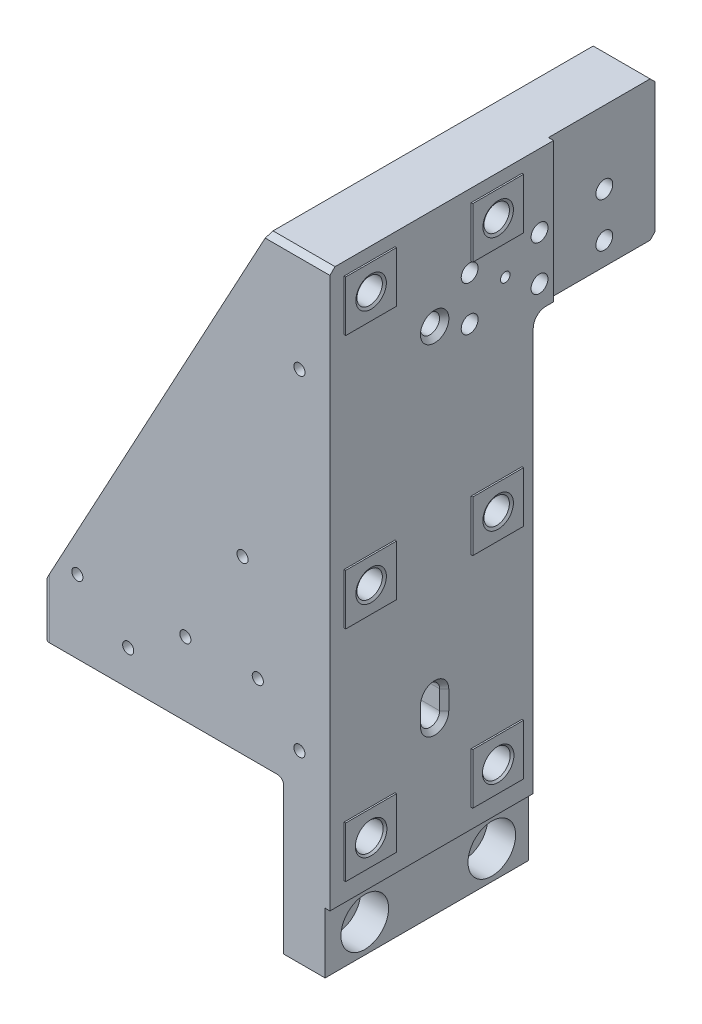
SolidWorks part; units mm, degrees
material "6061-T6 Al"
ref_plane "XY" through (0, 0, 0) normal (0, 0, 1) x (1, 0, 0)
ref_plane "XZ" through (0, 0, 0) normal (0, 1, 0) x (1, 0, 0)
ref_plane "YZ" through (0, 0, 0) normal (1, 0, 0) x (0, 0, -1)
sketch "Sketch1" plane through (0, 0, 0) normal (0, 0, 1) x (1, 0, 0)
  line L1 (0, 0) -> (25.4, 0)
  line L2 (0, 0) -> (0, 309.372)
  line L3 (0, 309.372) -> (25.4, 309.372)
  line L4 (25.4, 0) -> (25.4, 309.372)
  dimension "D1" = 309.372
  dimension "D2" = 25.4
extrude "Extrude1" add sketch "Sketch1" along normal blind 101.6
sketch "Sketch2" plane through (0, 0, 101.6) normal (0, 0, 1) x (1, 0, 0)
  line L0 (0, 309.372) -> (-6.35, 309.372)
  line L1 (-6.35, 309.372) -> (-118.745, 101.6)
  line L2 (-118.745, 101.6) -> (-118.745, 76.2)
  line L3 (-118.745, 76.2) -> (0, 76.2)
  line L4 (0, 76.2) -> (0, 309.372)
  line L5 (0, 309.372) -> (0, 0) construction
  line L6 (0, 0) -> (25.4, 0) construction
  dimension "D1" = 118.745
  dimension "D2" = 6.35
  dimension "D3" = 25.4
  dimension "D4" = 76.2
extrude "Extrude2" add sketch "Sketch2" against normal blind 53.975
sketch "Sketch7" plane through (0, 0, 0) normal (0, 0, -1) x (-1, 0, 0)
  line L0 (0, 76.2) -> (22.225, 76.2)
  line L1 (118.745, 76.2) -> (0, 76.2) construction
  line L2 (22.225, 76.2) -> (22.225, 280.0257)
  line L3 (0, 309.372) -> (0, 0) construction
  line L4 (0, 76.2) -> (0, 309.372)
  line L5 (0, 309.372) -> (6.35, 309.372)
  line L6 (6.35, 309.372) -> (22.225, 280.0257)
  line L7 (6.35, 309.372) -> (118.745, 101.6) construction
  dimension "D1" = 22.225
extrude "Extrude3" add sketch "Sketch7" against normal up to surface (47.625 mm away) up to face at (-48.133, 151.2316, 47.625)
sketch "Sketch3" plane through (0, 0, 101.6) normal (0, 0, 1) x (1, 0, 0)
  line L1 (25.4, 0) -> (22.225, 0)
  line L2 (25.4, 0) -> (25.4, 31.75)
  line L3 (25.4, 31.75) -> (22.225, 31.75)
  line L4 (22.225, 0) -> (22.225, 31.75)
  dimension "D1" = 31.75
  dimension "D2" = 3.175
extrude "Cut-Extrude1" cut sketch "Sketch3" against normal through all
hole_wizard "Lateral Holes CBORE for 1/2 Socket Head Cap Screw2" positions "Sketch40" profile "Sketch39" counterbore size "1/2" standard "Ansi Inch" end condition up to next
sketch "Sketch40" plane through (22.225, 0, 0) normal (1, 0, 0) x (0, 0, -1)
  line L0 (-101.6, 31.75) -> (-101.6, 309.372) construction
  line L1 (-101.6, 15.875) -> (0, 15.875) construction
  line L2 (-101.6, 31.75) -> (-101.6, 0) construction
  line L3 (0, 0) -> (0, 31.75) construction
  line L5 (0, 0) -> (-101.6, 0) construction
  point P0 (-81.788, 15.875)
  point P3 (-18.288, 15.875)
  dimension "D1" = 19.812
  dimension "D2" = 63.5
  dimension "D3" = 15.875
sketch "Sketch39" plane through (22.225, 15.875, 81.788) normal (0, 1, 0) x (0, 0, -1)
  line L0 (0, 0) -> (0, 22.225)
  line L1 (6.9469, 21.2979) -> (7.874, 22.225)
  line L2 (6.9469, 21.2979) -> (6.9469, 13.97)
  line L3 (6.9469, 13.97) -> (11.9126, 13.97)
  line L4 (11.9126, 13.97) -> (11.9126, 0)
  line L5 (11.9126, 0) -> (0, 0)
  line L11 (0, -6.35) -> (0, 107.95) construction
  line L12 (7.874, 22.225) -> (0, 22.225)
  line L13 (-6.9469, 21.2979) -> (-7.874, 22.225) construction
  dimension "Thru Hole Dia." = 13.8938
  dimension "Thru Hole Depth" = 22.225
  dimension "C'Bore Dia." = 23.8252
  dimension "C'Bore Depth" = 13.97
  dimension "Far C'Sink Dia." = 15.748
  dimension "Far C'Sink Angle" = 90
hole_wizard "Lateral Holes 1/2 Clearance Hole1" positions "Sketch42" profile "Sketch41" hole size "1/2" standard "Ansi Inch" end condition up to next
sketch "Sketch42" plane through (25.4, 0, 0) normal (1, 0, 0) x (0, 0, -1)
  line L0 (-101.6, 53.975) -> (0, 53.975) construction
  line L1 (-101.6, 31.75) -> (-101.6, 309.372) construction
  line L2 (0, 31.75) -> (0, 309.372) construction
  line L4 (0, 0) -> (-101.6, 0) construction
  point P0 (-18.288, 53.975)
  point P10 (-81.788, 53.975)
  dimension "D1" = 19.812
  dimension "D2" = 63.5
  dimension "D3" = 53.975
sketch "Sketch41" plane through (25.4, 53.975, 18.288) normal (0, 1, 0) x (0, 0, -1)
  line L0 (0, 0) -> (0, 25.4)
  line L1 (0, 25.4) -> (7.874, 25.4)
  line L2 (6.9456, 24.4716) -> (6.9456, 0.9284)
  line L3 (6.9456, 0.9284) -> (7.874, 0)
  line L5 (7.874, 0) -> (0, 0)
  line L6 (-6.9456, 0.9284) -> (-7.874, 0) construction
  line L7 (7.874, 25.4) -> (6.9456, 24.4716)
  line L8 (-7.874, 25.4) -> (-6.9456, 24.4716) construction
  line L11 (0, -6.35) -> (0, 107.95) construction
  dimension "Thru Hole Dia." = 13.8913
  dimension "Thru Hole Depth" = 25.4
  dimension "Near C'Sink Dia." = 15.748
  dimension "Near C'Sink Angle" = 90
  dimension "Far C'Sink Dia." = 15.748
  dimension "Far C'Sink Angle" = 90
hole_wizard "Lateral Holes 1/2-13 Tapped Hole1" positions "Sketch48" profile "Sketch47" tap size "1/2-13" standard "Ansi Inch"
sketch "Sketch48" plane through (25.4, 0, 0) normal (1, 0, 0) x (0, 0, -1)
  line L0 (-101.6, 290.322) -> (0, 290.322) construction
  line L1 (-101.6, 31.75) -> (-101.6, 309.372) construction
  line L2 (0, 31.75) -> (0, 309.372) construction
  line L6 (-101.6, 53.975) -> (0, 53.975) construction
  point P0 (-81.788, 290.322)
  point P14 (-18.288, 290.322)
  point P18 (-81.788, 163.322)
  point P20 (-18.288, 163.322)
  dimension "D1" = 236.347
  dimension "D2" = 19.812
  dimension "D3" = 63.5
  dimension "D4" = 127
sketch "Sketch47" plane through (25.4, 290.322, 81.788) normal (0, 1, 0) x (0, 0, -1)
  line L0 (0, 0) -> (0, 54.0195)
  line L1 (0, 54.0195) -> (5.3581, 50.8)
  line L2 (5.3581, 50.8) -> (5.3581, 38.1)
  line L3 (5.3581, 38.1) -> (6.35, 38.1)
  line L5 (6.35, 38.1) -> (6.35, 0.7332)
  line L6 (6.35, 0.7332) -> (7.62, 0)
  line L7 (7.62, 0) -> (0, 0)
  line L8 (-6.35, 0.7332) -> (-7.62, 0) construction
  line L10 (0, 54.0195) -> (-5.3581, 50.8) construction
  line L11 (0, -6.35) -> (0, 107.95) construction
  dimension "Tap Drill Dia." = 10.7163
  dimension "Tap Drill Depth" = 50.8
  dimension "Thread Major Dia." = 12.7
  dimension "Thread Depth" = 38.1
  dimension "Near C'Sink Dia." = 15.24
  dimension "Near C'Sink Angle" = 120
  dimension "Drill Angle" = 118
hole_wizard "Bracket Holes 1/2-13 Tapped Hole1" positions "Sketch44" profile "Sketch43" tap size "1/2-13" standard "Ansi Inch"
sketch "Sketch44" plane through (0, 76.2, 0) normal (0, -1, 0) x (1, 0, 0)
  line L0 (-101.6, 101.6) -> (-101.6, 47.625) construction
  line L1 (-118.745, 101.6) -> (0, 101.6) construction
  line L2 (-118.745, 47.625) -> (-22.225, 47.625) construction
  line L4 (-47.625, 101.6) -> (-47.625, 47.625) construction
  line L6 (-101.6, 88.9) -> (-47.625, 88.9) construction
  line L8 (-101.6, 60.325) -> (-47.625, 60.325) construction
  line L10 (0, 101.6) -> (0, 0) construction
  line L14 (25.4, 81.788) -> (-11.43, 81.788) construction
  line L15 (-11.43, 81.788) -> (-11.43, 64.3255) construction
  line L18 (25.4, 18.288) -> (-11.43, 18.288) construction
  line L19 (-11.43, 18.288) -> (-11.43, 35.7505) construction
  line L22 (0, 0) -> (0, 101.6) construction
  point P0 (-101.6, 60.325)
  point P14 (-101.6, 88.9)
  point P16 (-47.625, 88.9)
  point P18 (-47.625, 60.325)
  point P39 (-11.43, 64.3255)
  point P41 (-11.43, 35.7505)
  dimension "D1" = 53.975
  dimension "D2" = 28.575
  dimension "D3" = 47.625
  dimension "D4" = 12.7
  dimension "D5" = 11.43
  dimension "D6" = 28.575
sketch "Sketch43" plane through (-101.6, 76.2, 60.325) normal (1, 0, 0) x (0, 0, -1)
  line L0 (0, 0) -> (0, 47.6695)
  line L1 (0, 47.6695) -> (5.3581, 44.45)
  line L2 (5.3581, 44.45) -> (5.3581, 31.75)
  line L3 (5.3581, 31.75) -> (6.35, 31.75)
  line L5 (6.35, 31.75) -> (6.35, 0.7332)
  line L6 (6.35, 0.7332) -> (7.62, 0)
  line L7 (7.62, 0) -> (0, 0)
  line L8 (-6.35, 0.7332) -> (-7.62, 0) construction
  line L10 (0, 47.6695) -> (-5.3581, 44.45) construction
  line L11 (0, -6.35) -> (0, 107.95) construction
  dimension "Tap Drill Dia." = 10.7163
  dimension "Tap Drill Depth" = 44.45
  dimension "Thread Major Dia." = 12.7
  dimension "Thread Depth" = 31.75
  dimension "Near C'Sink Dia." = 15.24
  dimension "Near C'Sink Angle" = 120
  dimension "Drill Angle" = 118
hole_wizard "Pin Hole 3/8 (0.375) Diameter Hole3" positions "Sketch46" profile "Sketch45" counterbore size "3/8" standard "Ansi Inch"
sketch "Sketch46" plane through (0, 76.2, 0) normal (0, -1, 0) x (1, 0, 0)
  line L0 (-118.745, 101.6) -> (0, 101.6) construction
  line L1 (0, 0) -> (0, 101.6) construction
  point P0 (-76.2, 73.025)
  dimension "D1" = 28.575
  dimension "D2" = 76.2
sketch "Sketch45" plane through (-76.2, 76.2, 73.025) normal (1, 0, 0) x (0, 0, -1)
  line L0 (0, 0) -> (0, 21.9116)
  line L1 (0, 21.9116) -> (4.7625, 19.05)
  line L2 (4.7625, 19.05) -> (4.7625, 3.302)
  line L3 (4.7625, 3.302) -> (4.7879, 3.302)
  line L5 (4.7879, 3.302) -> (4.7879, 0.5461)
  line L6 (4.7879, 0.5461) -> (5.334, 0)
  line L7 (5.334, 0) -> (0, 0)
  line L8 (-4.7879, 0.5461) -> (-5.334, 0) construction
  line L10 (0, 21.9116) -> (-4.7625, 19.05) construction
  line L11 (0, -6.35) -> (0, 107.95) construction
  dimension "Hole Dia." = 9.525
  dimension "Hole Depth" = 19.05
  dimension "C'Bore Dia." = 9.5758
  dimension "C'Bore Depth" = 3.302
  dimension "Near C'Sink Dia." = 10.668
  dimension "Near C'Sink Angle" = 90
  dimension "Drill Angle" = 118
sketch "Sketch49" plane through (25.4, 0, 0) normal (1, 0, 0) x (0, 0, -1)
  line L0 (-101.6, 290.322) -> (0, 290.322) construction
  line L1 (-94.488, 303.022) -> (-69.088, 303.022)
  line L2 (-94.488, 303.022) -> (-94.488, 277.622)
  line L3 (-94.488, 277.622) -> (-69.088, 277.622)
  line L4 (-69.088, 303.022) -> (-69.088, 277.622)
  line L5 (-30.988, 303.022) -> (-5.588, 303.022)
  line L6 (-30.988, 303.022) -> (-30.988, 277.622)
  line L7 (-30.988, 277.622) -> (-5.588, 277.622)
  line L8 (-5.588, 303.022) -> (-5.588, 277.622)
  line L9 (-94.488, 66.675) -> (-69.088, 66.675)
  line L10 (-94.488, 66.675) -> (-94.488, 41.275)
  line L11 (-94.488, 41.275) -> (-69.088, 41.275)
  line L12 (-69.088, 66.675) -> (-69.088, 41.275)
  line L13 (-30.988, 66.675) -> (-5.588, 66.675)
  line L14 (-30.988, 66.675) -> (-30.988, 41.275)
  line L15 (-30.988, 41.275) -> (-5.588, 41.275)
  line L16 (-5.588, 66.675) -> (-5.588, 41.275)
  line L17 (-94.488, 176.022) -> (-69.088, 176.022)
  line L18 (-94.488, 176.022) -> (-94.488, 150.622)
  line L19 (-94.488, 150.622) -> (-69.088, 150.622)
  line L20 (-69.088, 176.022) -> (-69.088, 150.622)
  line L21 (-30.988, 176.022) -> (-5.588, 176.022)
  line L22 (-30.988, 176.022) -> (-30.988, 150.622)
  line L23 (-30.988, 150.622) -> (-5.588, 150.622)
  line L24 (-5.588, 176.022) -> (-5.588, 150.622)
  circle A2 centre (-81.788, 53.975) radius 7.874 construction
  circle A3 centre (-81.788, 53.975) radius 6.9456 construction
  circle A4 centre (-18.288, 53.975) radius 7.874 construction
  point P22 (-94.488, 290.322)
  point P32 (-94.488, 163.322)
  dimension "D8" = 12.7
  dimension "D1" = 12.7
  dimension "D2" = 12.7
  dimension "D3" = 25.4
  dimension "D4" = 25.4
  dimension "D5" = 25.4
  dimension "D6" = 25.4
extrude "Lateral Pads Extrude4" cut sketch "Sketch49" against normal blind 0.762 flip side to cut
hole_wizard "Thru Vent Holes 7/32 (0.21875) Diameter Hole1" positions "Sketch51" profile "Sketch52" hole size "7/32" standard "Ansi Inch" end condition through all
sketch "Sketch51" plane through (0, 0, 101.6) normal (0, 0, 1) x (1, 0, 0)
  line L8 (-118.745, 76.2) -> (0, 76.2) construction
  point P0 (-47.625, 114.3)
  point P17 (-101.6, 114.3)
  point P28 (-76.2, 95.25)
  point P36 (-11.43, 114.3)
  dimension "D1" = 38.1
  dimension "D5" = 19.05
sketch "Sketch52" plane through (-47.625, 114.3, 101.6) normal (1, 0, 0) x (0, -1, 0)
  line L0 (0, 0) -> (0, 101.6)
  line L1 (0, 101.6) -> (2.7781, 101.6)
  line L2 (2.7781, 101.6) -> (2.7781, 0)
  line L5 (2.7781, 0) -> (0, 0)
  line L11 (0, -6.35) -> (0, 107.95) construction
  dimension "Thru Hole Dia." = 5.5562
  dimension "Thru Hole Depth" = 101.6
hole_wizard "Blind Vent Hole 7/32 (0.21875) Diameter Hole3" positions "Sketch76" profile "Sketch75" hole size "7/32" standard "Ansi Inch"
sketch "Sketch76" plane through (0, 0, 101.6) normal (0, 0, 1) x (1, 0, 0)
  line L0 (25.4, 176.022) -> (25.4, 150.622) construction
  point P0 (-19.05, 163.322)
  dimension "D1" = 44.45
sketch "Sketch75" plane through (-19.05, 163.322, 101.6) normal (1, 0, 0) x (0, -1, 0)
  line L0 (0, 0) -> (0, 21.4813)
  line L1 (0, 21.4813) -> (2.7781, 19.812)
  line L2 (2.7781, 19.812) -> (2.7781, 0)
  line L5 (2.7781, 0) -> (0, 0)
  line L10 (0, 21.4813) -> (-2.7781, 19.812) construction
  line L11 (0, -6.35) -> (0, 107.95) construction
  dimension "Hole Dia." = 5.5562
  dimension "Hole Depth" = 19.812
  dimension "Drill Angle" = 118
hole_wizard "Pin Hole 3/8 (0.375) Diameter Hole4" positions "Sketch56" profile "Sketch55" hole size "3/8" standard "Ansi Inch"
sketch "Sketch56" plane through (24.638, 0, 0) normal (1, 0, 0) x (0, 0, -1)
  line L0 (-101.6, 309.372) -> (-101.6, 31.75) construction
  line L2 (0, 309.372) -> (-101.6, 309.372) construction
  point P0 (-49.276, 258.572)
  dimension "D1" = 52.324
  dimension "D2" = 50.8
sketch "Sketch55" plane through (24.638, 258.572, 49.276) normal (0, 1, 0) x (0, 0, -1)
  line L0 (0, 0) -> (0, 21.9169)
  line L1 (0, 21.9169) -> (4.7714, 19.05)
  line L2 (4.7714, 19.05) -> (4.7714, 2.3406)
  line L3 (4.7714, 2.3406) -> (7.112, 0)
  line L5 (7.112, 0) -> (0, 0)
  line L6 (-4.7714, 2.3406) -> (-7.112, 0) construction
  line L10 (0, 21.9169) -> (-4.7714, 19.05) construction
  line L11 (0, -6.35) -> (0, 107.95) construction
  dimension "Hole Dia." = 9.5428
  dimension "Hole Depth" = 19.05
  dimension "Near C'Sink Dia." = 14.224
  dimension "Near C'Sink Angle" = 90
  dimension "Drill Angle" = 118
sketch "Sketch57" plane through (24.638, 0, 0) normal (1, 0, 0) x (0, 0, -1)
  line L0 (-49.276, 98.2345) -> (-49.276, 88.7095) construction
  line L1 (-44.5046, 98.2345) -> (-44.5046, 88.7095)
  line L2 (-54.0474, 98.2345) -> (-54.0474, 88.7095)
  line L4 (-101.6, 309.372) -> (-101.6, 31.75) construction
  line L5 (0, 309.372) -> (-101.6, 309.372) construction
  arc A0 (-44.5046, 98.2345) -> (-54.0474, 98.2345) centre (-49.276, 98.2345) ccw
  arc A1 (-54.0474, 88.7095) -> (-44.5046, 88.7095) centre (-49.276, 88.7095) ccw
  point P2 (-49.276, 93.472)
  dimension "D2" = 4.7714
  dimension "D1" = 9.525
  dimension "D3" = 215.9
  dimension "D4" = 52.324
extrude "Pin Slot Extrude5" cut sketch "Sketch57" against normal blind 19.05
chamfer "Pin Slot Chamfer5" distance 2.286 angle 45 4 edges at (24.638, 93.472, 44.5046) (24.638, 83.9381, 49.276) (24.638, 93.472, 54.0474) (24.638, 103.0059, 49.276)
sketch "Sketch58" plane through (0, 309.372, 0) normal (0, 1, 0) x (1, 0, 0)
  line L0 (24.638, 0) -> (-6.35, 0) construction
  line L1 (-6.731, 0) -> (-22.479, 0)
  line L2 (-6.731, 0) -> (-6.731, -47.625)
  line L3 (-6.731, -47.625) -> (-22.479, -47.625)
  line L4 (-22.479, 0) -> (-22.479, -47.625)
  line L5 (-22.225, -47.625) -> (-118.745, -47.625) construction
  line L6 (24.638, 0) -> (24.638, -101.6) construction
  dimension "D1" = 31.369
  dimension "D2" = 15.748
extrude "Cut-Extrude2" cut sketch "Sketch58" against normal blind 76.2
sketch "Sketch59" plane through (0, 0, 0) normal (0, 0, -1) x (-1, 0, 0)
  line L0 (6.35, 309.372) -> (6.731, 308.6677)
  line L1 (-24.638, 309.372) -> (6.35, 309.372)
  line L2 (-24.638, 309.372) -> (-24.638, 239.522)
  line L3 (-24.638, 239.522) -> (6.731, 239.522)
  line L4 (6.731, 308.6677) -> (6.731, 239.522)
  dimension "D1" = 69.85
extrude "Extrude4" add sketch "Sketch59" along normal blind 63.5
hole_wizard "Tapped Hole for 5/16-18 Helicoil1" positions "Sketch61" profile "Sketch60" tap size "5/16-18" standard "Helicoil® Inch" end condition through all
sketch "Sketch61" plane through (-6.731, 0, 0) normal (-1, 0, 0) x (0, 0, 1)
  point P0 (-38.0746, 273.1008)
  dimension "D1" = 273.1008
  dimension "D2" = 38.0746
sketch "Sketch60" plane through (-6.731, 273.1008, -38.0746) normal (0, 1, 0) x (0, 0, 1)
  line L0 (0, 0) -> (0, 32.131)
  line L1 (0, 32.131) -> (4.2164, 32.131)
  line L3 (4.2164, 32.131) -> (4.2164, 19.2634)
  line L4 (4.9327, 19.2634) -> (4.2164, 19.2634)
  line L5 (4.9327, 19.2634) -> (4.9327, 0.635)
  line L6 (4.9327, 0.635) -> (5.5677, 0)
  line L7 (5.5677, 0) -> (0, 0)
  line L8 (-4.9327, 0.635) -> (-5.5677, 0) construction
  line L11 (0, -6.35) -> (0, 107.95) construction
  dimension "Thru Tap Drill Dia." = 8.4328
  dimension "Thru Tap Drill Depth" = 32.131
  dimension "Thread Major Dia." = 9.8654
  dimension "Thread Depth" = 19.2634
  dimension "Near C'Sink Dia." = 11.1354
  dimension "Near C'Sink Angle" = 90
pattern_linear "LPattern1" count 3 spacing 34.925 along (0, 0, 1) count 2 spacing 22.225 along (0, -1, 0) of "Tapped Hole for 5/16-18 Helicoil1"
chamfer "Chamfer7" distance 2.54 angle 45 4 edges at (8.9535, 239.522, -63.5) (9.144, 309.372, -63.5) (9.144, 309.372, 101.6) (-14.478, 233.172, 0)
sketch "Sketch62" plane through (24.638, 0, 0) normal (1, 0, 0) x (0, 0, -1)
  line L0 (60.96, 309.372) -> (-99.06, 309.372) construction
  line L1 (63.5, 309.372) -> (10.16, 309.372)
  line L2 (63.5, 309.372) -> (63.5, 239.522)
  line L3 (63.5, 239.522) -> (10.16, 239.522)
  line L4 (10.16, 309.372) -> (10.16, 239.522)
  line L5 (60.96, 239.522) -> (0, 239.522) construction
  line L6 (63.5, 306.832) -> (63.5, 242.062) construction
  dimension "D1" = 53.34
extrude "Extrude5" cut sketch "Sketch62" against normal blind 2.54
hole_wizard "7/32 (0.21875) Diameter Hole2" positions "Sketch67" profile "Sketch66" hole size "7/32" standard "Ansi Inch"
sketch "Sketch67" plane through (0, 0, 101.6) normal (0, 0, 1) x (1, 0, 0)
  line L0 (9.398, 258.572) -> (9.398, 93.472) construction
  line L2 (24.638, 306.832) -> (24.638, 31.75) construction
  point P0 (9.398, 258.572)
  point P1 (9.398, 93.472)
  dimension "D1" = 15.24
sketch "Sketch66" plane through (9.398, 258.572, 101.6) normal (1, 0, 0) x (0, -1, 0)
  line L0 (0, 0) -> (0, 52.4693)
  line L1 (0, 52.4693) -> (2.7781, 50.8)
  line L2 (2.7781, 50.8) -> (2.7781, 0)
  line L5 (2.7781, 0) -> (0, 0)
  line L10 (0, 52.4693) -> (-2.7781, 50.8) construction
  line L11 (0, -6.35) -> (0, 107.95) construction
  dimension "Hole Dia." = 5.5562
  dimension "Hole Depth" = 50.8
  dimension "Drill Angle" = 118
hole_wizard "1/4 (0.25) Diameter Hole1" positions "Sketch69" profile "Sketch68" hole size "1/4" standard "Ansi Inch"
sketch "Sketch69" plane through (-6.731, 0, 0) normal (-1, 0, 0) x (0, 0, 1)
  circle A0 centre (-38.0746, 273.1008) radius 5.5677 construction
  circle A1 centre (-38.0746, 273.1008) radius 4.2164 construction
  point P0 (13.97, 262.255)
  dimension "D1" = 52.0446
  dimension "D2" = 10.8458
sketch "Sketch68" plane through (-6.731, 262.255, 13.97) normal (0, 1, 0) x (0, 0, 1)
  line L0 (0, 0) -> (0, 14.6131)
  line L1 (0, 14.6131) -> (3.1839, 12.7)
  line L2 (3.1839, 12.7) -> (3.1839, 1.6421)
  line L3 (3.1839, 1.6421) -> (4.826, 0)
  line L5 (4.826, 0) -> (0, 0)
  line L6 (-3.1839, 1.6421) -> (-4.826, 0) construction
  line L10 (0, 14.6131) -> (-3.1839, 12.7) construction
  line L11 (0, -6.35) -> (0, 107.95) construction
  dimension "Hole Dia." = 6.3678
  dimension "Hole Depth" = 12.7
  dimension "Near C'Sink Dia." = 9.652
  dimension "Near C'Sink Angle" = 90
  dimension "Drill Angle" = 118
sketch "Sketch70" plane through (-6.731, 0, 0) normal (-1, 0, 0) x (0, 0, 1)
  line L0 (-66.675, 262.255) -> (-53.975, 262.255) construction
  line L1 (-66.675, 265.4389) -> (-53.975, 265.4389)
  line L2 (-66.675, 259.0711) -> (-53.975, 259.0711)
  line L3 (-60.96, 239.522) -> (0, 239.522) construction
  line L4 (101.6, 306.832) -> (101.6, 101.6) construction
  arc A0 (-66.675, 265.4389) -> (-66.675, 259.0711) centre (-66.675, 262.255) ccw
  arc A1 (-53.975, 259.0711) -> (-53.975, 265.4389) centre (-53.975, 262.255) ccw
  point P2 (-60.325, 262.255)
  dimension "D3" = 3.1839
  dimension "D1" = 161.925
  dimension "D2" = 12.7
extrude "Extrude6" cut sketch "Sketch70" against normal blind 12.7
chamfer "Chamfer8" distance 1.651 angle 45 3 edges at (-6.731, 259.0711, -58.7375) (-6.731, 262.255, -50.7911) (-6.731, 265.4389, -58.7375)
hole_wizard "3/16 (0.1875) Diameter Hole1" positions "Sketch72" profile "Sketch71" hole size "3/16" standard "Ansi Inch" end condition through all
sketch "Sketch72" plane through (-6.731, 0, 0) normal (-1, 0, 0) x (0, 0, 1)
  circle A0 centre (13.97, 262.255) radius 4.826 construction
  point P0 (13.97, 262.255)
sketch "Sketch71" plane through (-6.731, 262.255, 13.97) normal (0, 1, 0) x (0, 0, 1)
  line L0 (0, 0) -> (0, 32.131)
  line L1 (0, 32.131) -> (2.3812, 32.131)
  line L2 (2.3812, 32.131) -> (2.3812, 0)
  line L5 (2.3812, 0) -> (0, 0)
  line L11 (0, -6.35) -> (0, 107.95) construction
  dimension "Thru Hole Dia." = 4.7625
  dimension "Thru Hole Depth" = 32.131
fillet "Fillet2" radius 1.5875 1 edges
fillet "Fillet3" radius 3.175 2 edges at (-118.745, 88.9, 47.625) (-118.745, 88.9, 101.6)
chamfer "Chamfer10" distance 1.524 angle 45 13 edges at (-68.8975, 76.2, 47.625) (-117.8151, 76.2, 48.5549) (-118.745, 76.2, 74.6125) (-117.8151, 76.2, 100.6701) (-0.465, 75.735, 0) (-0.465, 75.735, 101.6) (0, 37.3062, 0) (-11.9062, 76.2, 0) (11.1125, 0, 0) (11.1125, 0, 101.6) (22.225, 0, 50.8)
fillet "Fillet4" radius 6.35 2 edges at (-14.478, 233.172, 47.625)
chamfer "Chamfer11" distance 2.286 angle 45 1 edges at (0, 0, 50.8)
